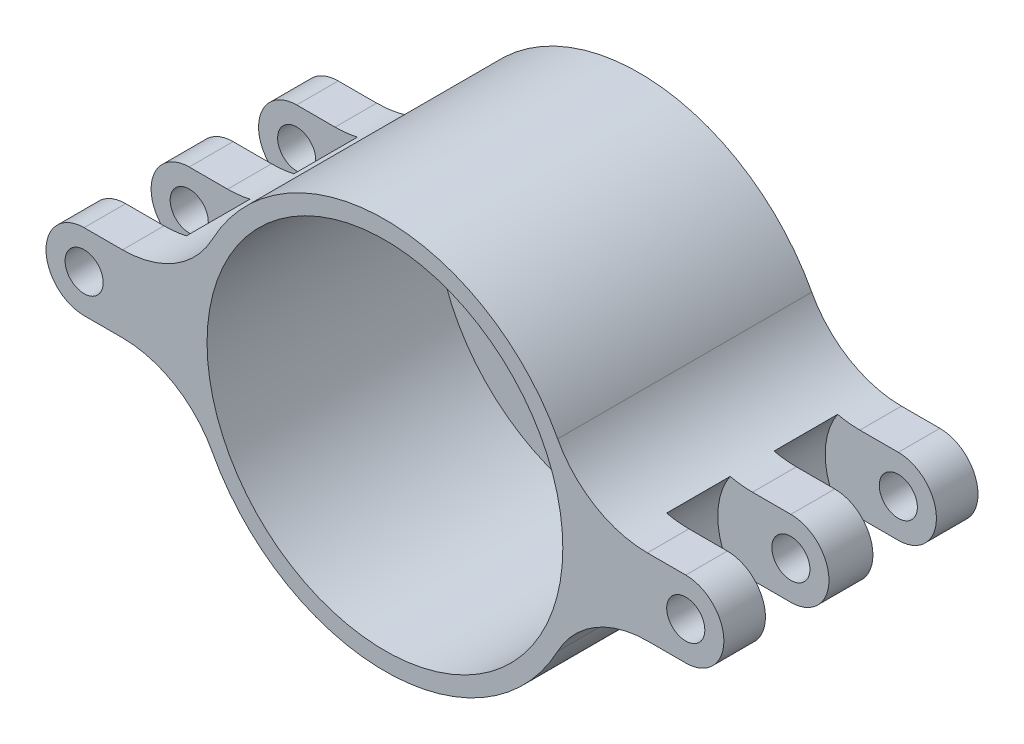
SolidWorks part; units mm, degrees
ref_plane "Front Plane" through (0, 0, 0) normal (0, 0, 1) x (1, 0, 0)
ref_plane "Top Plane" through (0, 0, 0) normal (0, 1, 0) x (1, 0, 0)
ref_plane "Right Plane" through (0, 0, 0) normal (1, 0, 0) x (0, 0, -1)
sketch "Sketch1" plane through (0, 0, 0) normal (0, 0, 1) x (1, 0, 0)
  line L0 (0, 0) -> (-35.6343, 0) construction
  line L1 (-14, 0) -> (-18.675, 0) construction
  circle A0 centre (0, 0) radius 15.4
  circle A1 centre (-23.675, 0) radius 1.5 construction
  circle A2 centre (-23.675, 0) radius 5 construction
  circle A7 centre (0, 0) radius 14 construction
  circle A10 centre (0, 0) radius 28.675 construction
  circle A12 centre (-23.675, 0) radius 5.75 construction
  point P4 (-7.7, -13.3368)
  point P10 (0, 0)
  point P13 (0, 0)
  point P14 (-7.7, 13.3368)
  point P15 (15.4, 0)
  point P16 (32.5084, 33.0381)
  point P17 (0, 0)
  point P18 (0, 0)
  point P19 (0, 0)
  point P20 (0, 0)
  point P21 (0, 0)
  point P22 (0, 0)
  point P23 (0, 0)
  point P24 (0, 0)
  point P25 (0, 0)
  point P26 (0, 0)
  point P34 (0, 0)
  point P35 (0, 0)
  point P36 (0, 0)
  point P37 (0, 0)
  point P39 (0, 0)
  dimension "D2" = 3
  dimension "D3" = 10
  dimension "D10" = 11.5
extrude "Boss-Extrude1" add sketch "Sketch1" along normal blind 20
sketch "Sketch6" plane through (0, 0, 20) normal (0, 0, 1) x (1, 0, 0)
  line L1 (-23.675, 3) -> (-15.105, 3)
  line L2 (-23.675, -3) -> (-15.105, -3)
  arc A0 (-23.675, 3) -> (-23.675, -3) centre (-23.675, 0) ccw
  circle A1 centre (0, 0) radius 15.4 construction
  arc A2 (-15.105, 3) -> (-15.105, -3) centre (0, 0) ccw
  dimension "D1" = 6
extrude "Boss-Extrude2" add sketch "Sketch6" against normal up to surface (20 mm away) up to face at (15.4, 0, 0)
fillet "Fillet4" radius 8 2 edges at (-15.105, -3, 10) (-15.105, 3, 10)
pattern_circular "CirPattern11" count 2 over 360 about axis through (0, 0, 0) along (0, 0, 1) of "Fillet4", "Boss-Extrude2"
sketch "Sketch4" plane through (0, 0, 20) normal (0, 0, 1) x (1, 0, 0)
  circle A0 centre (0, 0) radius 14 construction
  circle A1 centre (0, 0) radius 14
extrude "Cut-Extrude3" cut sketch "Sketch4" against normal offset from surface (18 mm away) 2
sketch "Sketch5" plane through (0, 0, 2) normal (0, 0, 1) x (1, 0, 0)
  circle A0 centre (0, 0) radius 5
  dimension "D1" = 10
extrude "Cut-Extrude4" cut sketch "Sketch5" against normal through all both and the other way through all
sketch "Sketch7" plane through (0, 0, 2) normal (0, 0, 1) x (1, 0, 0)
  line L0 (200000, 0) -> (-200035.6343, 0) construction
  line L1 (-5.4, 0) -> (-5, 0) construction
  circle A0 centre (-8.4, 0) radius 3
  circle A2 centre (0, 0) radius 5 construction
  dimension "D1" = 0.4
  dimension "D2" = 6
extrude "Cut-Extrude5" cut sketch "Sketch7" against normal through all both and the other way through all
pattern_circular "CirPattern12" count 4 over 360 about axis through (0, 0, 0) along (0, 0, 1) of "Cut-Extrude5"
sketch "Sketch2" plane through (0, 0, 20) normal (0, 0, 1) x (1, 0, 0)
  circle A2 centre (-23.675, 0) radius 1.5 construction
  circle A5 centre (-23.675, 0) radius 1.5
  point P10 (-0.25, -0.1443)
extrude "Cut-Extrude1" cut sketch "Sketch2" against normal through all both and the other way through all
pattern_circular "CirPattern10" count 2 over 360 about axis through (0, 0, 0) along (0, 0, 1) of "Cut-Extrude1"
ref_plane "roller plane" through (0, 0, 5.7716) normal (0, 0, 1) x (1, 0, 0)
sketch "Sketch3" plane through (0, 0, 5.7716) normal (0, 0, 1) x (1, 0, 0)
  circle A0 centre (-23.675, 0) radius 5.75 construction
  circle A1 centre (-23.675, 0) radius 5.75
extrude "Cut-Extrude2" cut sketch "Sketch3" against normal mid plane 5
pattern_circular "CirPattern3" count 2 over 360 about axis through (0, 0, 0) along (0, 0, 1) of "Cut-Extrude2"
ref_plane "mid plane" through (0, 0, 10) normal (0, 0, 1) x (1, 0, 0)
mirror "Mirror1" about plane through (0, 0, 10) normal (0, 0, 1) of "Cut-Extrude2", "CirPattern3"
equation "\"flex_pitch_dia\"= 56mm'flex spline pitch diameter"
equation "\"circ_pitch_dia\"= 62.05mm'circular spline pitch diameter (desired diameter after deformation)"
equation "\"clearence\"= 0.8mm"
equation "\"flex_inner_circ_to_pitch_dia\"= 1.55mm'distance between \"cup\" and pitch circle"
equation "\"wave_drive_dia\"= \"circ_pitch_dia\" - 2 * \"flex_inner_circ_to_pitch_dia\" - 2 * \"clearence\""
equation "\"D6@Sketch1\"= \"wave_drive_dia\""
equation "\"bearing_dia\"= 10mm"
equation "\"D3@Sketch1\"= \"bearing_dia\""
equation "\"D10@Sketch1\"= \"bearing_dia\" + 1.5"
equation "\"embedded_motor_dia\"= 28mm"
equation "\"D5@Sketch1\"= \"embedded_motor_dia\""
equation "\"lobes\" = 2"
